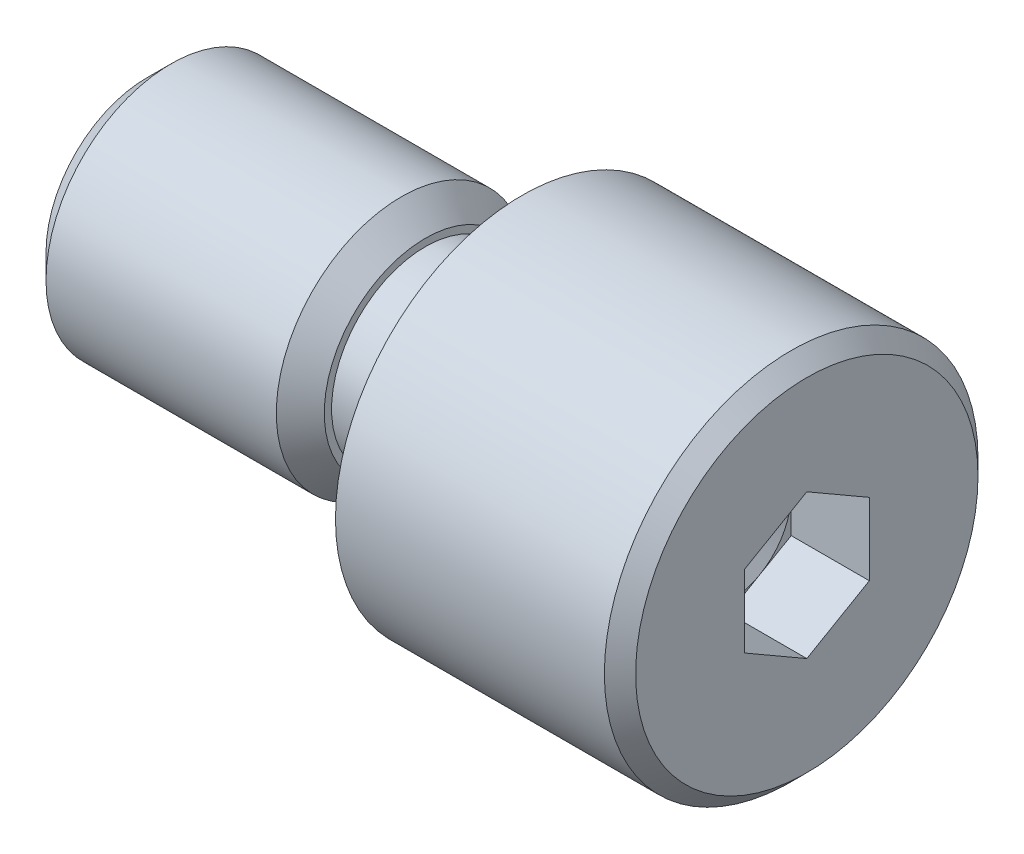
SolidWorks part; units mm, degrees
material "Cast Stainless Steel"
ref_plane "X-Y Datum" through (0, 0, 0) normal (0, 0, 1) x (1, 0, 0)
ref_plane "X-Z Datum" through (0, 0, 0) normal (0, 1, 0) x (1, 0, 0)
ref_plane "Y-Z Datum" through (0, 0, 0) normal (1, 0, 0) x (0, 0, -1)
sketch "Sketch1" plane through (0, 0, 0) normal (0, 0, 1) x (1, 0, 0)
  line L0 (0, 4) -> (0, 0)
  line L1 (0, 0) -> (21.1, 0)
  line L2 (21.1, 0) -> (21.1, 5.975)
  line L3 (21.1, 5.975) -> (12, 5.975)
  line L4 (12, 5.975) -> (12, 3)
  line L5 (12, 3) -> (8.9, 3)
  line L6 (8.9, 3) -> (8.9, 4)
  line L7 (8.9, 4) -> (0, 4)
  line L8 (0, 0) -> (21.1, 0) construction
revolve "Revolve1" add sketch "Sketch1" angle 360 about L8
sketch "Sketch2" plane through (21.1, 0, 0) normal (1, 0, 0) x (0, 0, -1)
  line L0 (0, -2.3094) -> (2, -1.1547)
  line L1 (2, -1.1547) -> (2, 1.1547)
  line L2 (2, 1.1547) -> (0, 2.3094)
  line L3 (0, 2.3094) -> (-2, 1.1547)
  line L4 (-2, 1.1547) -> (-2, -1.1547)
  line L5 (-2, -1.1547) -> (0, -2.3094)
extrude "Cut-Extrude1" cut sketch "Sketch2" against normal blind 2.5
ref_plane "Plane1" through (0, 0, 0) normal (0, 0, -1) x (-1, 0, 0)
sketch "Sketch3" plane through (0, 0, 0) normal (0, 0, -1) x (-1, 0, 0)
  line L0 (-18.6, 2) -> (-18.6, 0)
  line L1 (-18.6, 0) -> (-17.4453, 0)
  line L2 (-17.4453, 0) -> (-18.6, 2)
  line L3 (-18.6, 0) -> (-17.4453, 0) construction
revolve "Cut-Revolve1" cut sketch "Sketch3" angle 360 about L3
chamfer "Chamfer1" distance 0.767 angle 45 2 edges at (0, 0, -4) (8.9, 0, -4)
chamfer "Chamfer2" distance 0.5 angle 45 1 edges at (21.1, 0, -5.975)
fillet "Fillet1" radius 0.2 1 edges at (12, 0, -3)
